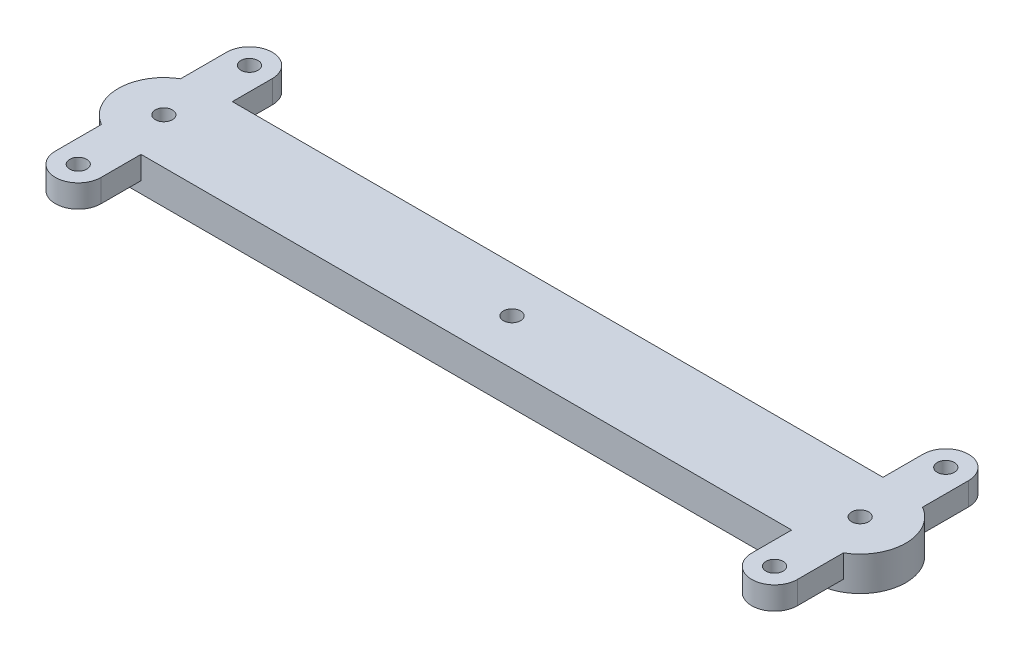
SolidWorks part; units mm, degrees
ref_plane "Front Plane" through (0, 0, 0) normal (0, 0, 1) x (1, 0, 0)
ref_plane "Top Plane" through (0, 0, 0) normal (0, 1, 0) x (1, 0, 0)
ref_plane "Right Plane" through (0, 0, 0) normal (1, 0, 0) x (0, 0, -1)
sketch "Sketch1" plane through (0, 0, 0) normal (0, 1, 0) x (1, 0, 0)
  line L0 (0, 0) -> (122, 0) construction
  line L1 (0, 0) -> (122, 0) construction
  line L2 (0, 8) -> (122, 8)
  line L3 (0, -8) -> (122, -8)
  circle A0 centre (0, 0) radius 1.5
  circle A1 centre (122, 0) radius 1.5
  arc A2 (0, 8) -> (0, -8) centre (0, 0) ccw
  arc A3 (122, -8) -> (122, 8) centre (122, 0) ccw
  point P5 (61, 0)
  dimension "D1" = 122
extrude "Boss-Extrude1" add sketch "Sketch1" along normal blind 6 contours A1 | L3 A3 L2 A2 | A0
sketch "Sketch2" plane through (0, 6, 0) normal (0, 1, 0) x (1, 0, 0)
  line L0 (0, 0) -> (0, 15) construction
  line L1 (0, 0) -> (0, -15) construction
  line L2 (0, 15) -> (0, -15) construction
  line L3 (4, 15) -> (4, -15)
  line L4 (-4, 15) -> (-4, -15)
  line L5 (61, 8) -> (61, 30.2748) construction
  line L6 (0, 8) -> (122, 8) construction
  line L7 (122, 15) -> (122, -15) construction
  line L8 (118, 15) -> (118, -15)
  line L9 (126, 15) -> (126, -15)
  circle A0 centre (0, 15) radius 1.5
  circle A1 centre (0, -15) radius 1.5
  arc A2 (4, 15) -> (-4, 15) centre (0, 15) ccw
  arc A3 (-4, -15) -> (4, -15) centre (0, -15) ccw
  arc A4 (118, 15) -> (126, 15) centre (122, 15) cw
  arc A5 (126, -15) -> (118, -15) centre (122, -15) cw
  circle A6 centre (122, 15) radius 1.5
  circle A7 centre (122, -15) radius 1.5
  circle A8 centre (0, 0) radius 1.5
  point P6 (0, 0)
  point P17 (122, 0)
  line M14 (0, -8) -> (122, -8)
  arc M15 (122, -8) -> (122, 8) centre (122, 0) ccw
  line M16 (122, 8) -> (0, 8)
  dimension "D1" = 15
  dimension "D2" = 15
extrude "Boss-Extrude2" add sketch "Sketch2" against normal blind 4 contours A4 L8 L9 A6 M16 M15 | A5 L9 L8 A7 M15 M14 | L4 A3 L3 A2 | A1 | A0 | A8
sketch "Sketch3" plane through (0, 6, 0) normal (0, 1, 0) x (1, 0, 0)
  line L0 (61, 8) -> (61, -8) construction
  line L1 (4, 8) -> (118, 8) construction
  line L2 (4, -8) -> (118, -8) construction
  circle A0 centre (61, 0) radius 1.5
extrude "Cut-Extrude1" cut sketch "Sketch3" against normal blind 10
